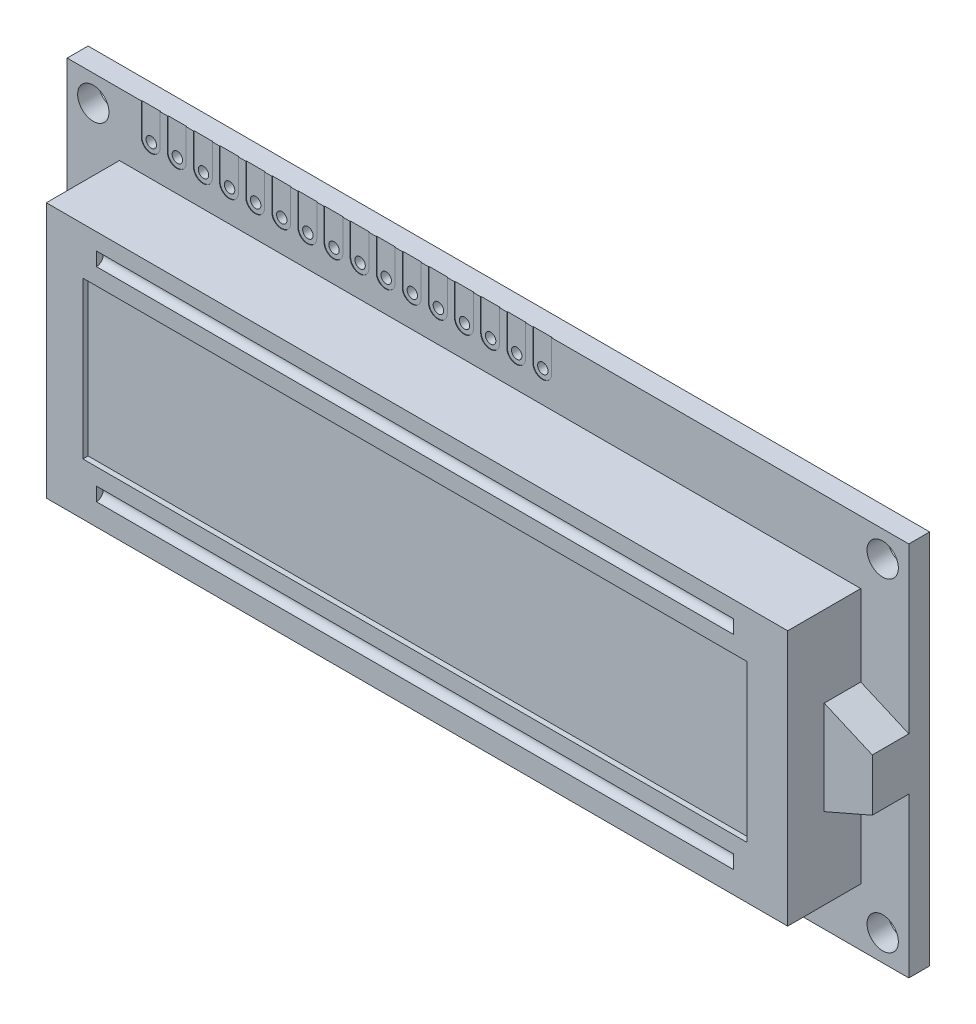
SolidWorks part; units mm, degrees
ref_plane "Alzado" through (0, 0, 0) normal (0, 0, 1) x (1, 0, 0)
ref_plane "Planta" through (0, 0, 0) normal (0, 1, 0) x (1, 0, 0)
ref_plane "Vista lateral" through (0, 0, 0) normal (1, 0, 0) x (0, 0, -1)
sketch "Croquis1" plane through (0, 0, 0) normal (0, 0, 1) x (1, 0, 0)
  line L0 (0, 0) -> (0, 8.4176) construction
  line L1 (-40.3, 18) -> (40.3, 18)
  line L2 (-40.3, 18) -> (-40.3, -18)
  line L3 (-40.3, -18) -> (40.3, -18)
  line L4 (40.3, 18) -> (40.3, -18)
  line L5 (-40.3, 18) -> (40.3, -18) construction
  line L6 (-40.3, -18) -> (40.3, 18) construction
  line L7 (0, 0) -> (-8.4257, 0) construction
  circle A0 centre (37.8, 15.5) radius 1.5
  circle A1 centre (-37.8, 15.5) radius 1.5
  circle A2 centre (37.8, -15.5) radius 1.5
  circle A3 centre (-37.8, -15.5) radius 1.5
  point P0 (0, 0)
  dimension "D3" = 2.5
  dimension "D1" = 80.6
  dimension "D2" = 36
  dimension "D4" = 2.5
extrude "Saliente-Extruir1" add sketch "Croquis1" along normal blind 2
sketch "Croquis2" plane through (0, 0, 2) normal (0, 0, 1) x (1, 0, 0)
  line L5 (-40.3, 18) -> (-40.3, -18) construction
  line L6 (-35.3, 12) -> (35.7, 12)
  line L7 (-35.3, 12) -> (-35.3, -12.5)
  line L8 (-35.3, -12.5) -> (35.7, -12.5)
  line L9 (35.7, 12) -> (35.7, -12.5)
  line L10 (-35.3, 12) -> (35.7, -12.5) construction
  line L11 (-35.3, -12.5) -> (35.7, 12) construction
  line L12 (-40.3, -18) -> (40.3, -18) construction
  point P0 (0.2, -0.25)
  dimension "D1" = 71
  dimension "D2" = 24.5
  dimension "D3" = 5
  dimension "D4" = 5.5
extrude "Saliente-Extruir2" add sketch "Croquis2" along normal blind 7
sketch "Croquis3" plane through (0, 0, 9) normal (0, 0, 1) x (1, 0, 0)
  line L0 (-35.3, 12) -> (-35.3, -12.5) construction
  line L1 (-31.8, 7.5) -> (31.8, 7.5)
  line L2 (-31.8, 7.5) -> (-31.8, -7.5)
  line L3 (-31.8, -7.5) -> (31.8, -7.5)
  line L4 (31.8, 7.5) -> (31.8, -7.5)
  line L5 (-31.8, 7.5) -> (31.8, -7.5) construction
  line L6 (-31.8, -7.5) -> (31.8, 7.5) construction
  line L7 (-35.3, -12.5) -> (35.7, -12.5) construction
  point P0 (0, 0)
  dimension "D1" = 3.5
  dimension "D2" = 5
extrude "Cortar-Extruir1" cut sketch "Croquis3" against normal blind 0.5
sketch "Croquis4" plane through (0, 0, 0) normal (1, 0, 0) x (0, 0, -1)
  line L0 (-9, 12) -> (-9, 7.5) construction
  line L1 (0, 0) -> (-6.02, 0) construction
  line L2 (-9, 10.4014) -> (-9, 9.0981)
  line L3 (-9, -10.4014) -> (-9, -9.0981)
  arc A0 (-9, 9.0986) -> (-9, 10.4014) centre (-9, 9.75) ccw
  arc A1 (-9, -9.0986) -> (-9, -10.4014) centre (-9, -9.75) cw
extrude "Cortar-Extruir2" cut sketch "Croquis4" against normal blind 30.5 and the other way blind 30.5 contours L2 A0 | A1 L3
sketch "Croquis5" plane through (0, 0, 2) normal (0, 0, 1) x (1, 0, 0)
  line L0 (35.7, -0.25) -> (40.3, -0.25) construction
  line L3 (35.7, -12.5) -> (35.7, 12) construction
  line L4 (35.7, 4.25) -> (40.3, 2.25)
  line L5 (40.3, -18) -> (40.3, 18) construction
  line L6 (40.3, 2.25) -> (40.3, -2.75)
  line L7 (35.7, -4.75) -> (35.7, 4.25)
  line L8 (35.7, -4.75) -> (40.3, -2.75)
  dimension "D1" = 2.5
  dimension "D2" = 4.5
extrude "Saliente-Extruir3" add sketch "Croquis5" along normal blind 3.5
sketch "Croquis6" plane through (0, 0, 2) normal (0, 0, 1) x (1, 0, 0)
  line L0 (40.3, 18) -> (-40.3, 18) construction
  line L2 (-37.8, 17) -> (-37.8, 14) construction
  circle A0 centre (-32.3, 15) radius 0.5
  circle A1 centre (-37.8, 15.5) radius 1.5 construction
  circle A2 centre (-29.8, 15) radius 0.5
  circle A3 centre (-27.3, 15) radius 0.5
  circle A4 centre (-24.8, 15) radius 0.5
  circle A5 centre (-22.3, 15) radius 0.5
  circle A6 centre (-19.8, 15) radius 0.5
  circle A7 centre (-17.3, 15) radius 0.5
  circle A8 centre (-14.8, 15) radius 0.5
  circle A9 centre (-12.3, 15) radius 0.5
  circle A10 centre (-9.8, 15) radius 0.5
  circle A11 centre (-7.3, 15) radius 0.5
  circle A12 centre (-4.8, 15) radius 0.5
  circle A13 centre (-2.3, 15) radius 0.5
  circle A14 centre (0.2, 15) radius 0.5
  circle A15 centre (2.7, 15) radius 0.5
  circle A16 centre (5.2, 15) radius 0.5
  point P6 (-37.8, 15.5)
  dimension "D1" = 3
  dimension "D2" = 5.5
  dimension "D3" = 16
extrude "Cortar-Extruir3" cut sketch "Croquis6" against normal blind 3.5
sketch "Croquis8" plane through (0, 0, 2) normal (0, 0, 1) x (1, 0, 0)
  line L0 (-33.2, 15) -> (-33.2, 18)
  line L1 (40.3, 18) -> (-40.3, 18) construction
  line L2 (-31.4, 15) -> (-31.4, 18)
  line L3 (-31.4, 18) -> (-33.2, 18)
  circle A0 centre (-32.3, 15) radius 0.5 construction
  circle A1 centre (-32.3, 15) radius 0.5
  arc A2 (-33.2, 15) -> (-31.4, 15) centre (-32.3, 15) ccw
  circle A3 centre (-32.3, 15) radius 0.9 construction
  dimension "D1" = 0.4
extrude "Cortar-Extruir4" cut sketch "Croquis8" against normal blind 0.05
pattern_linear "MatrizL1" count 16 spacing 2.5 along (1, 0, 0) of "Cortar-Extruir4"
